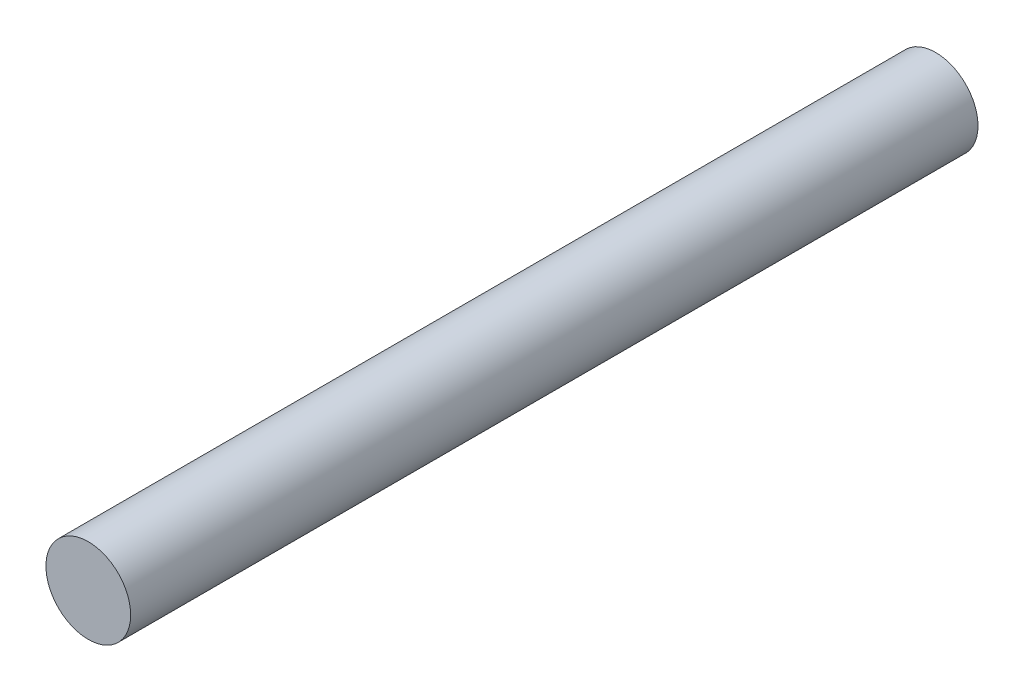
SolidWorks part; units mm, degrees
ref_plane "Front Plane" through (0, 0, 0) normal (0, 0, 1) x (1, 0, 0)
ref_plane "Top Plane" through (0, 0, 0) normal (0, 1, 0) x (1, 0, 0)
ref_plane "Right Plane" through (0, 0, 0) normal (1, 0, 0) x (0, 0, -1)
sketch "Sketch1" plane through (0, 0, 0) normal (0, 0, 1) x (1, 0, 0)
  circle A0 centre (0, 0) radius 2
  dimension "D1" = 4
extrude "Boss-Extrude1" add sketch "Sketch1" along normal blind 40 contours A0
